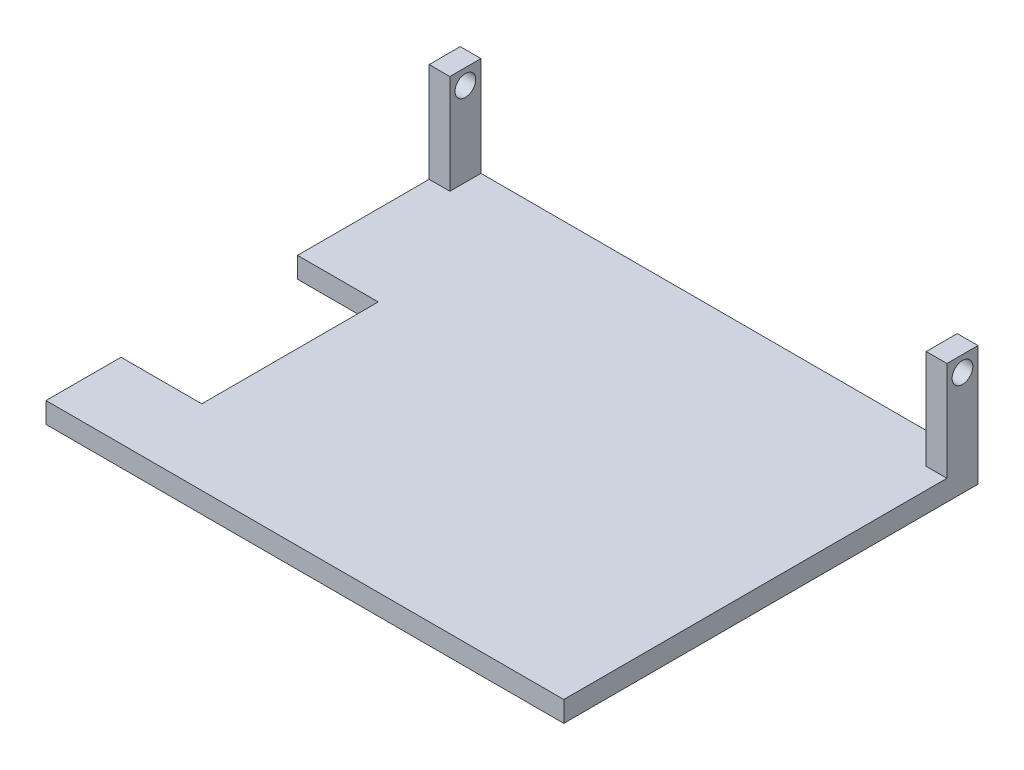
SolidWorks part; units mm, degrees
ref_plane "Plan de face" through (0, 0, 0) normal (0, 0, 1) x (1, 0, 0)
ref_plane "Plan de dessus" through (0, 0, 0) normal (0, 1, 0) x (1, 0, 0)
ref_plane "Plan de droite" through (0, 0, 0) normal (1, 0, 0) x (0, 0, -1)
sketch "Esquisse1" plane through (0, 0, 0) normal (0, 1, 0) x (1, 0, 0)
  line L0 (-210, 0) -> (-250, 0)
  line L1 (0, 0) -> (-210, 0)
  line L2 (0, 0) -> (0, 200)
  line L3 (0, 200) -> (-211.0248, 200)
  line L4 (-250, 0) -> (-250, 36.2289)
  line L5 (-250, 36.2289) -> (-211.0248, 36.2289)
  line L6 (-211.0248, 36.2289) -> (-211.0248, 121.4421)
  line L7 (-211.0248, 121.4421) -> (-250, 121.4421)
  line L8 (-250, 121.4421) -> (-250, 200)
  line L9 (-250, 200) -> (-211.0248, 200)
  dimension "D1" = 200
  dimension "D2" = 210
  dimension "D3" = 40
extrude "Boss.-Extru.1" add sketch "Esquisse1" along normal blind 10
sketch "Esquisse2" plane through (0, 0, 0) normal (1, 0, 0) x (0, 0, -1)
  line L0 (0, 10) -> (200, 10) construction
  line L1 (185, 10) -> (200, 10)
  line L2 (185, 10) -> (185, 58)
  line L3 (185, 58) -> (200, 58)
  line L4 (200, 10) -> (200, 58)
  line L5 (200, 10) -> (200, 0) construction
  dimension "D1" = 15
  dimension "D2" = 48
extrude "Boss.-Extru.2" add sketch "Esquisse2" against normal blind 250
sketch "Esquisse5" plane through (0, 0, -185) normal (0, 0, 1) x (1, 0, 0)
  line L0 (-250, 10) -> (0, 10) construction
  line L1 (-240, 10) -> (-10, 10)
  line L2 (-240, 10) -> (-240, 58)
  line L3 (-240, 58) -> (-10, 58)
  line L4 (-10, 10) -> (-10, 58)
  line L5 (-250, 58) -> (0, 58) construction
  line L6 (-250, 58) -> (-250, 10) construction
  line L7 (0, 58) -> (0, 10) construction
  point P8 (-250, 34)
  dimension "D1" = 10
  dimension "D2" = 10
extrude "Enlèv. mat.-Extru.1" cut sketch "Esquisse5" against normal blind 15
sketch "Esquisse6" plane through (0, 0, 0) normal (1, 0, 0) x (0, 0, -1)
  line L0 (185, 58) -> (185, 10) construction
  line L1 (200, 58) -> (185, 58) construction
  circle A0 centre (192.5, 50.5) radius 5
  dimension "D1" = 10
  dimension "D2" = 7.5
  dimension "D3" = 7.5
extrude "Enlèv. mat.-Extru.2" cut sketch "Esquisse6" against normal blind 250
